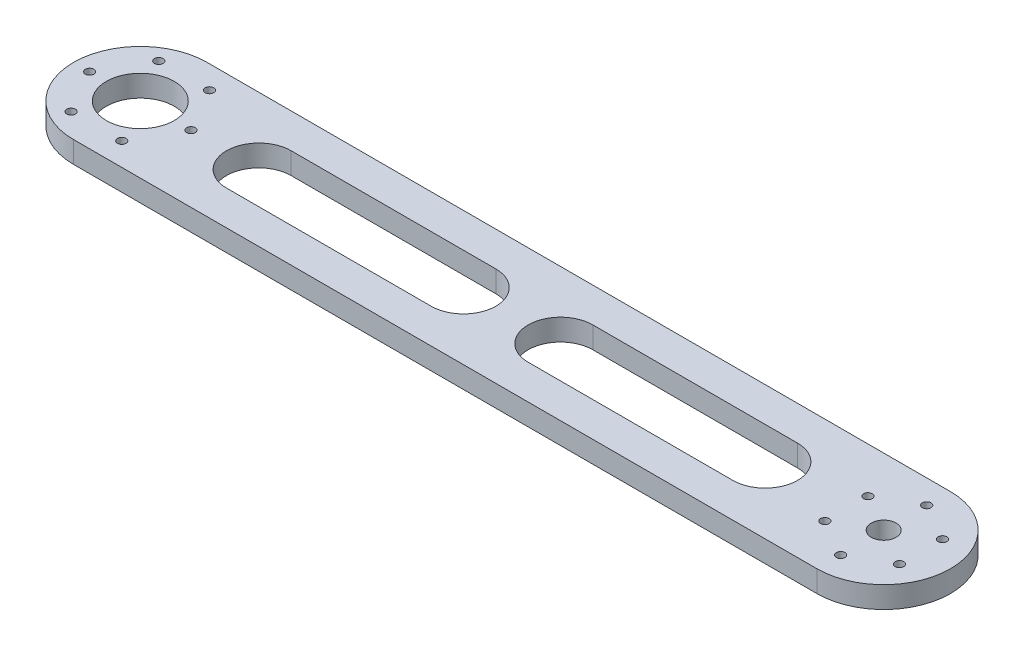
SolidWorks part; units mm, degrees
material "Acrylic (Medium-high impact)"
ref_plane "Front Plane" through (0, 0, 0) normal (0, 0, 1) x (1, 0, 0)
ref_plane "Top Plane" through (0, 0, 0) normal (0, 1, 0) x (1, 0, 0)
ref_plane "Right Plane" through (0, 0, 0) normal (1, 0, 0) x (0, 0, -1)
sketch "Sketch1" plane through (0, 0, 0) normal (0, 1, 0) x (1, 0, 0)
  line L0 (-132.6984, 0) -> (-79.0625, 0) construction
  line L1 (-104.5467, 31) -> (240.4533, 31)
  line L2 (-104.5467, -31) -> (240.4533, -31)
  line L3 (240.4533, 0) -> (218.7722, -12.5176) construction
  line L4 (-49.5467, 15) -> (45.4533, 15)
  line L5 (-49.5467, -15) -> (45.4533, -15)
  line L6 (220.4533, 0) -> (237.5348, 0) construction
  line L7 (90.4533, 15) -> (185.4533, 15)
  line L8 (90.4533, -15) -> (185.4533, -15)
  line L9 (-152.9281, 0) -> (131.6241, 0) construction
  arc A0 (-104.5467, 31) -> (-104.5467, -31) centre (-104.5467, 0) ccw
  arc A1 (240.4533, -31) -> (240.4533, 31) centre (240.4533, 0) ccw
  circle A2 centre (240.4533, 0) radius 5.75
  circle A3 centre (-104.5467, 0) radius 15.75
  circle A4 centre (240.4533, 0) radius 20 construction
  circle A5 centre (223.1328, -10) radius 2
  circle A6 centre (223.1249, 9.9863) radius 2
  circle A7 centre (240.4296, 19.9863) radius 2
  circle A8 centre (257.7423, 10) radius 2
  circle A9 centre (257.7501, -9.9863) radius 2
  circle A10 centre (240.4454, -19.9863) radius 2
  circle A11 centre (-104.5467, 0) radius 23.5 construction
  circle A12 centre (-128.0467, 0) radius 2
  circle A13 centre (-116.3006, 20.3448) radius 2
  circle A14 centre (-92.8085, 20.3448) radius 2
  circle A15 centre (-81.0625, 0) radius 2
  circle A16 centre (-92.8085, -20.3448) radius 2
  circle A17 centre (-116.3006, -20.3448) radius 2
  arc A18 (-49.5467, 15) -> (-49.5467, -15) centre (-49.5467, 0) ccw
  arc A19 (185.4533, -15) -> (185.4533, 15) centre (185.4533, 0) ccw
  arc A20 (45.4533, -15) -> (45.4533, 15) centre (45.4533, 0) ccw
  arc A21 (90.4533, 15) -> (90.4533, -15) centre (90.4533, 0) ccw
  point P40 (-104.5546, 0)
  point P41 (240.4375, 0)
  point P45 (238.4375, 0)
  dimension "D1" = 62
  dimension "D2" = 62
  dimension "D4" = 11.5
  dimension "D5" = 31.5
  dimension "D6" = 40
  dimension "D7" = 30
  dimension "D9" = 47
  dimension "D10" = 4
  dimension "D8" = 4
  dimension "D13" = 30
  dimension "D14" = 30
  dimension "D15" = 30
  dimension "D16" = 30
  dimension "D3" = 345
  dimension "D12" = 6
  dimension "D17" = 55
  dimension "D18" = 55
  dimension "D19" = 95
  dimension "D20" = 95
  dimension "D11" = 6
extrude "Boss-Extrude1" add sketch "Sketch1" along normal blind 10
